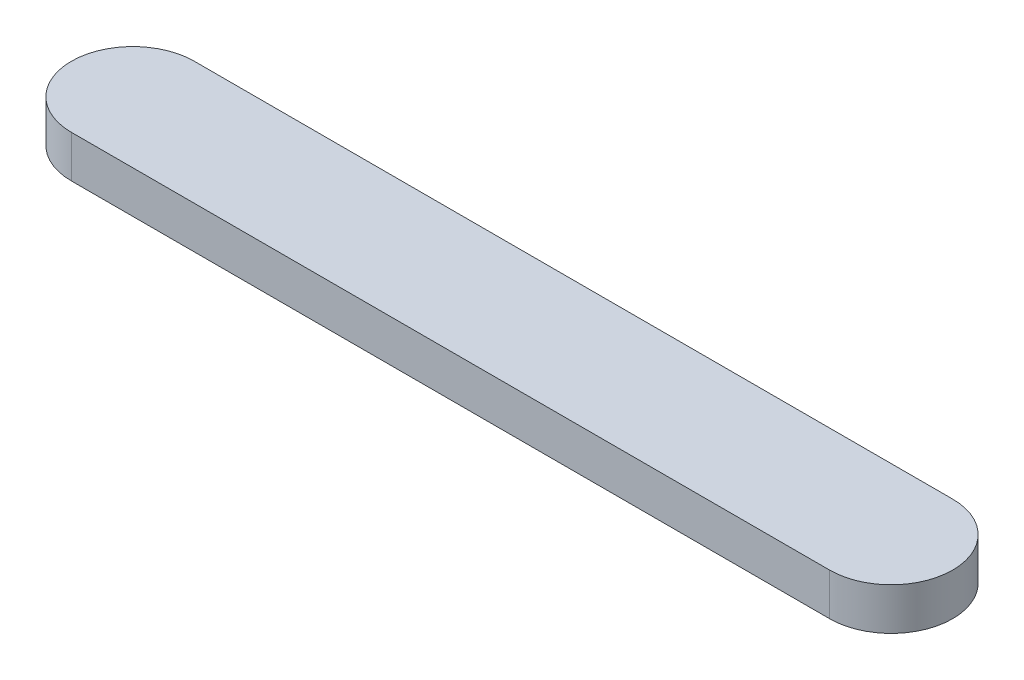
SolidWorks part; units mm, degrees
ref_plane "Front Plane" through (0, 0, 0) normal (0, 0, 1) x (1, 0, 0)
ref_plane "Top Plane" through (0, 0, 0) normal (0, 1, 0) x (1, 0, 0)
ref_plane "Right Plane" through (0, 0, 0) normal (1, 0, 0) x (0, 0, -1)
sketch "Sketch1" plane through (0, 0, 0) normal (0, 1, 0) x (1, 0, 0)
  line L0 (0, 0) -> (90, 0) construction
  line L1 (0, 7.3) -> (90, 7.3)
  line L2 (0, -7.3) -> (90, -7.3)
  arc A0 (0, 7.3) -> (0, -7.3) centre (0, 0) ccw
  arc A1 (90, -7.3) -> (90, 7.3) centre (90, 0) ccw
  point P3 (45, 0)
  point P8 (-7.3, 0)
  point P9 (97.3, 0)
  dimension "D1" = 104.6
  dimension "D2" = 14.6
extrude "Boss-Extrude1" add sketch "Sketch1" along normal blind 5
